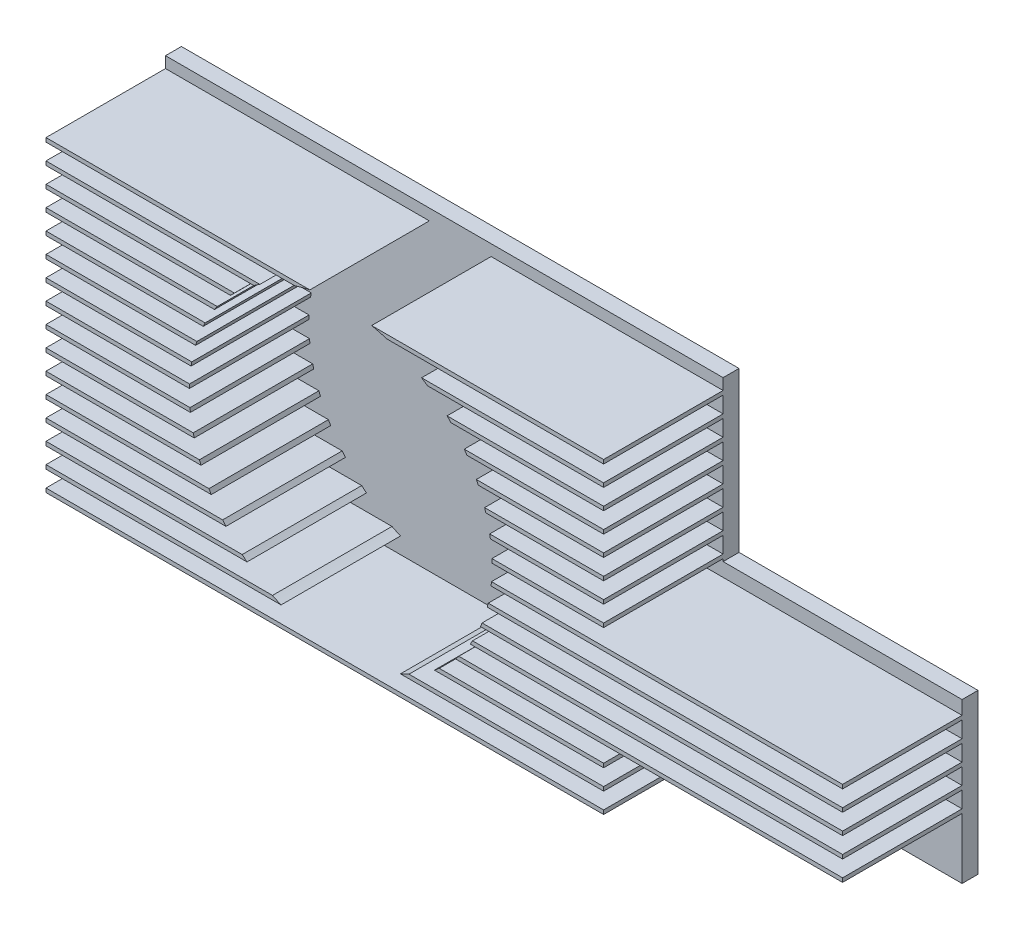
SolidWorks part; units mm, degrees
ref_plane "Plan de face" through (0, 0, 0) normal (0, 0, 1) x (1, 0, 0)
ref_plane "Plan de dessus" through (0, 0, 0) normal (0, 1, 0) x (1, 0, 0)
ref_plane "Plan de droite" through (0, 0, 0) normal (1, 0, 0) x (0, 0, -1)
sketch "Main-Sketch" plane through (0, 0, 0) normal (0, 0, 1) x (1, 0, 0)
  line L1 (0, 0) -> (100, 0)
  line L2 (0, 0) -> (0, 40)
  line L3 (0, 40) -> (100, 40)
  line L4 (100, 0) -> (100, 40)
  dimension "D1" = 100
  dimension "D2" = 40
extrude "Main" add sketch "Main-Sketch" along normal blind 2
sketch "Esquisse2" plane through (0, 0, 2) normal (0, 0, 1) x (1, 0, 0)
  line L1 (0, 0.5) -> (100, 0.5)
  line L2 (0, 0.5) -> (0, 0)
  line L3 (0, 0) -> (100, 0)
  line L4 (100, 0.5) -> (100, 0)
  point P4 (100, 0)
  point P6 (0, 0)
  dimension "D1" = 0.5
extrude "Boss.-Extru.2" add sketch "Esquisse2" along normal blind 15
pattern_linear "Répétition linéaire2" count 16 spacing 2.54 along (0, 1, 0) of "Boss.-Extru.2"
sketch "Esquisse3" plane through (0, 0, 2) normal (0, 0, 1) x (1, 0, 0)
  line L1 (70, 7.5) -> (100, 7.5)
  line L2 (70, 7.5) -> (70, 0)
  line L3 (70, 0) -> (100, 0)
  line L4 (100, 7.5) -> (100, 0)
  point P10 (70.7461, 20)
  point P11 (70, 20.32)
  point P12 (70, 15.74)
  point P13 (72.0833, 15.74)
  dimension "D1" = 30
  dimension "D2" = 7.5
extrude "Enlèv. mat.-Extru.1" cut sketch "Esquisse3" along normal through all
sketch "Esquisse4" plane through (0, 0, 2) normal (0, 0, 1) x (1, 0, 0)
  line L0 (70, 3.04) -> (70, 2.54) construction
  line L1 (100, 40) -> (70, 40)
  line L2 (100, 40) -> (100, 20)
  line L3 (100, 20) -> (70, 20)
  line L4 (70, 40) -> (70, 20)
  dimension "D1" = 20
extrude "Enlèv. mat.-Extru.2" cut sketch "Esquisse4" against normal mid plane 50
sketch "Esquisse5" plane through (0, 0, 2) normal (0, 0, 1) x (1, 0, 0)
  line L0 (0, 20.32) -> (0, 18.28) construction
  line L1 (70, 40) -> (0, 40) construction
  circle A0 centre (37, 20) radius 19
  dimension "D1" = 38
  dimension "D2" = 37
  dimension "D3" = 20
extrude "Enlèv. mat.-Extru.3" cut sketch "Esquisse5" along normal through all
